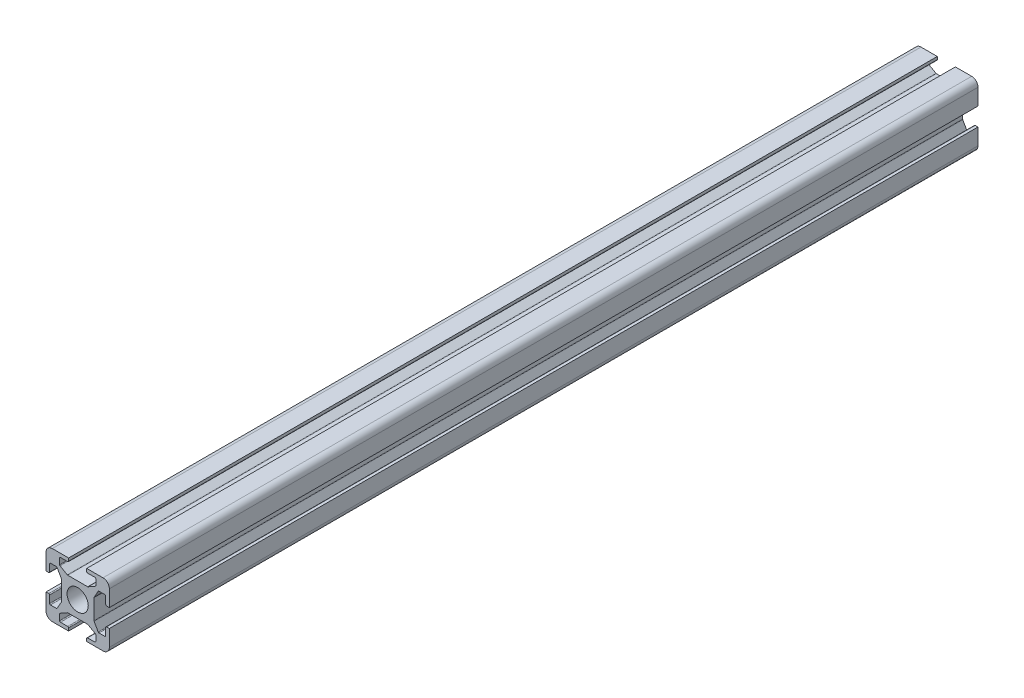
SolidWorks part; units mm, degrees
ref_plane "Alzado" through (0, 0, 0) normal (0, 0, 1) x (1, 0, 0)
ref_plane "Planta" through (0, 0, 0) normal (0, 1, 0) x (1, 0, 0)
ref_plane "Vista lateral" through (0, 0, 0) normal (1, 0, 0) x (0, 0, -1)
sketch "Croquis1" plane through (0, 0, 0) normal (0, 0, 1) x (1, 0, 0)
  line L0 (-10, 0) -> (10, 0) construction
  line L1 (0, 32.431) -> (0, -32.431) construction
  line L2 (-17.5, -5) -> (-16, -5)
  line L3 (-15.5, -15.5) -> (15.5, -15.5) construction
  line L4 (-15.5, -15.5) -> (-15.5, 15.5) construction
  line L5 (17.5, -17.5) -> (17.5, 17.5) construction
  line L6 (-17.5, -17.5) -> (17.5, 17.5) construction
  line L7 (-17.5, 17.5) -> (17.5, -17.5) construction
  line L8 (9, -9) -> (-9, -9) construction
  line L9 (9, -9) -> (9, 9) construction
  line L10 (9, 9) -> (-9, 9) construction
  line L11 (-9, -9) -> (-9, 9) construction
  line L12 (9, -9) -> (-9, 9) construction
  line L13 (9, 9) -> (-9, -9) construction
  line L14 (-15.5, 15.5) -> (15.5, 15.5) construction
  line L15 (15.5, -15.5) -> (15.5, 15.5) construction
  line L16 (-15.5, -15.5) -> (15.5, 15.5) construction
  line L17 (-15.5, 15.5) -> (15.5, -15.5) construction
  line L18 (-14.0807, -14.0828) -> (13.915, 13.9172) construction
  line L19 (-9, 15.5) -> (9, 15.5)
  line L20 (-15.5, -5.5) -> (-15.5, -9.5)
  line L21 (-15, -10) -> (-11.7901, -10)
  line L22 (-11.356, -9.7481) -> (-9.0659, -5.7407)
  line L23 (-9, -5.4926) -> (-9, 5.4926)
  line L24 (-11.356, 9.7481) -> (-9.0659, 5.7407)
  line L25 (-15, 10) -> (-11.7901, 10)
  line L26 (-15.5, 5.5) -> (-15.5, 9.5)
  line L27 (-17.5, 5) -> (-16, 5)
  line L28 (-17.5, 14) -> (-17.5, 5)
  line L29 (-17.5, -5) -> (-17.5, -14)
  line L30 (5, 17.5) -> (5, 16)
  line L31 (-17.5, 17.5) -> (17.5, 17.5) construction
  line L32 (5.5, 15.5) -> (9.5, 15.5)
  line L33 (10, 15) -> (10, 11.7901)
  line L34 (-17.5, -17.5) -> (17.5, -17.5) construction
  line L35 (9.7481, 11.356) -> (5.7407, 9.0659)
  line L36 (-17.5, -17.5) -> (-17.5, 17.5) construction
  line L37 (-17.5, 17.5) -> (17.5, 17.5) construction
  line L38 (17.5, -17.5) -> (17.5, 17.5) construction
  line L39 (-17.5, -17.5) -> (17.5, 17.5) construction
  line L40 (-17.5, 17.5) -> (17.5, -17.5) construction
  line L41 (-5.4926, 9) -> (5.4926, 9)
  line L42 (-9.7481, 11.356) -> (-5.7407, 9.0659)
  line L43 (-10, 15) -> (-10, 11.7901)
  line L44 (-10, -10) -> (10, 10) construction
  line L45 (-10, 10) -> (10, -10) construction
  line L46 (-5.5, 15.5) -> (-9.5, 15.5)
  line L47 (-5, 17.5) -> (-5, 16)
  line L48 (-14, -14) -> (14, 14) construction
  line L49 (-14, 14) -> (14, -14) construction
  line L50 (17.5, -5) -> (16, -5)
  line L51 (15.5, -5.5) -> (15.5, -9.5)
  line L52 (15, -10) -> (11.7901, -10)
  line L53 (11.356, -9.7481) -> (9.0659, -5.7407)
  line L54 (9, 5.4926) -> (9, -5.4926)
  line L55 (11.356, 9.7481) -> (9.0659, 5.7407)
  line L56 (15, 10) -> (11.7901, 10)
  line L57 (15.5, 5.5) -> (15.5, 9.5)
  line L58 (17.5, 5) -> (16, 5)
  line L59 (-5, -17.5) -> (-5, -16)
  line L60 (-5.5, -15.5) -> (-9.5, -15.5)
  line L61 (-10, -15) -> (-10, -11.7901)
  line L62 (-9.7481, -11.356) -> (-5.7407, -9.0659)
  line L63 (5.4926, -9) -> (-5.4926, -9)
  line L64 (9.7481, -11.356) -> (5.7407, -9.0659)
  line L65 (10, -15) -> (10, -11.7901)
  line L66 (5.5, -15.5) -> (9.5, -15.5)
  line L67 (5, -17.5) -> (5, -16)
  line L68 (-5, 17.5) -> (-14, 17.5)
  line L69 (5, 17.5) -> (14, 17.5)
  line L70 (17.5, 14) -> (17.5, 5)
  line L71 (17.5, -5) -> (17.5, -14)
  line L72 (14, -17.5) -> (5, -17.5)
  line L73 (-14, -17.5) -> (-5, -17.5)
  circle A0 centre (0, 0) radius 5.85
  arc A1 (-9.0659, -5.7407) -> (-9, -5.4926) centre (-9.5, -5.4926) ccw
  arc A2 (-11.7901, -10) -> (-11.356, -9.7481) centre (-11.7901, -9.5) ccw
  arc A3 (-15.5, -9.5) -> (-15, -10) centre (-15, -9.5) ccw
  arc A4 (-16, -5) -> (-15.5, -5.5) centre (-16, -5.5) cw
  arc A5 (-11.7901, 10) -> (-11.356, 9.7481) centre (-11.7901, 9.5) cw
  arc A6 (-15.5, 9.5) -> (-15, 10) centre (-15, 9.5) cw
  arc A7 (-16, 5) -> (-15.5, 5.5) centre (-16, 5.5) ccw
  arc A8 (-9.0659, 5.7407) -> (-9, 5.4926) centre (-9.5, 5.4926) cw
  arc A9 (5, 16) -> (5.5, 15.5) centre (5.5, 16) ccw
  arc A10 (9.5, 15.5) -> (10, 15) centre (9.5, 15) cw
  arc A11 (10, 11.7901) -> (9.7481, 11.356) centre (9.5, 11.7901) cw
  arc A12 (5.7407, 9.0659) -> (5.4926, 9) centre (5.4926, 9.5) cw
  arc A13 (-5.7407, 9.0659) -> (-5.4926, 9) centre (-5.4926, 9.5) ccw
  arc A14 (-10, 11.7901) -> (-9.7481, 11.356) centre (-9.5, 11.7901) ccw
  arc A15 (-9.5, 15.5) -> (-10, 15) centre (-9.5, 15) ccw
  arc A16 (-5, 16) -> (-5.5, 15.5) centre (-5.5, 16) cw
  arc A17 (16, -5) -> (15.5, -5.5) centre (16, -5.5) ccw
  arc A18 (15.5, -9.5) -> (15, -10) centre (15, -9.5) cw
  arc A19 (11.7901, -10) -> (11.356, -9.7481) centre (11.7901, -9.5) cw
  arc A20 (9.0659, -5.7407) -> (9, -5.4926) centre (9.5, -5.4926) cw
  arc A21 (9.0659, 5.7407) -> (9, 5.4926) centre (9.5, 5.4926) ccw
  arc A22 (11.7901, 10) -> (11.356, 9.7481) centre (11.7901, 9.5) ccw
  arc A23 (15.5, 9.5) -> (15, 10) centre (15, 9.5) ccw
  arc A24 (16, 5) -> (15.5, 5.5) centre (16, 5.5) cw
  arc A25 (-5, -16) -> (-5.5, -15.5) centre (-5.5, -16) ccw
  arc A26 (-9.5, -15.5) -> (-10, -15) centre (-9.5, -15) cw
  arc A27 (-10, -11.7901) -> (-9.7481, -11.356) centre (-9.5, -11.7901) cw
  arc A28 (-5.7407, -9.0659) -> (-5.4926, -9) centre (-5.4926, -9.5) cw
  arc A29 (5.7407, -9.0659) -> (5.4926, -9) centre (5.4926, -9.5) ccw
  arc A30 (10, -11.7901) -> (9.7481, -11.356) centre (9.5, -11.7901) ccw
  arc A31 (9.5, -15.5) -> (10, -15) centre (9.5, -15) ccw
  arc A32 (5, -16) -> (5.5, -15.5) centre (5.5, -16) cw
  arc A33 (17.5, -14) -> (14, -17.5) centre (14, -14) cw
  arc A34 (14, 17.5) -> (17.5, 14) centre (14, 14) cw
  arc A35 (-14, 17.5) -> (-17.5, 14) centre (-14, 14) ccw
  arc A36 (-17.5, -14) -> (-14, -17.5) centre (-14, -14) ccw
  point P0 (0, 0)
  point P4 (0, 0)
  point P31 (0, 0)
  point P37 (-11.5, -10)
  point P48 (-15.5, -10)
  point P50 (0, -15.5)
  point P53 (-9, 0)
  point P56 (0, 15.5172)
  point P149 (0, 0)
  dimension "D3" = 11.7
  dimension "D11" = 0.5
  dimension "D12" = 4
  dimension "D13" = 3.5
  dimension "D14" = 3.5
  dimension "D1" = 35
  dimension "D2" = 35
  dimension "D4" = 18
  dimension "D5" = 18
  dimension "D6" = 31
  dimension "D7" = 10
  dimension "D8" = 20
  dimension "D9" = 4
  dimension "D10" = 35
extrude "Saliente-Extruir1" add sketch "Croquis1" along normal blind 480 contours L29 A36 L73 L59 A25 L60 A26 L61 A27 L62 A28 L63 A29 L64 A30 L65 A31 L66 A32 L67 L72 A33 L71 L50 A17 L51 A18 L52 A19 L53 A20 L54 A21 L55 A22 L56 A23 L57 A24 L58 L70 A34 L69 L30 A9 L19 L32 A10 L33 A11 L35
